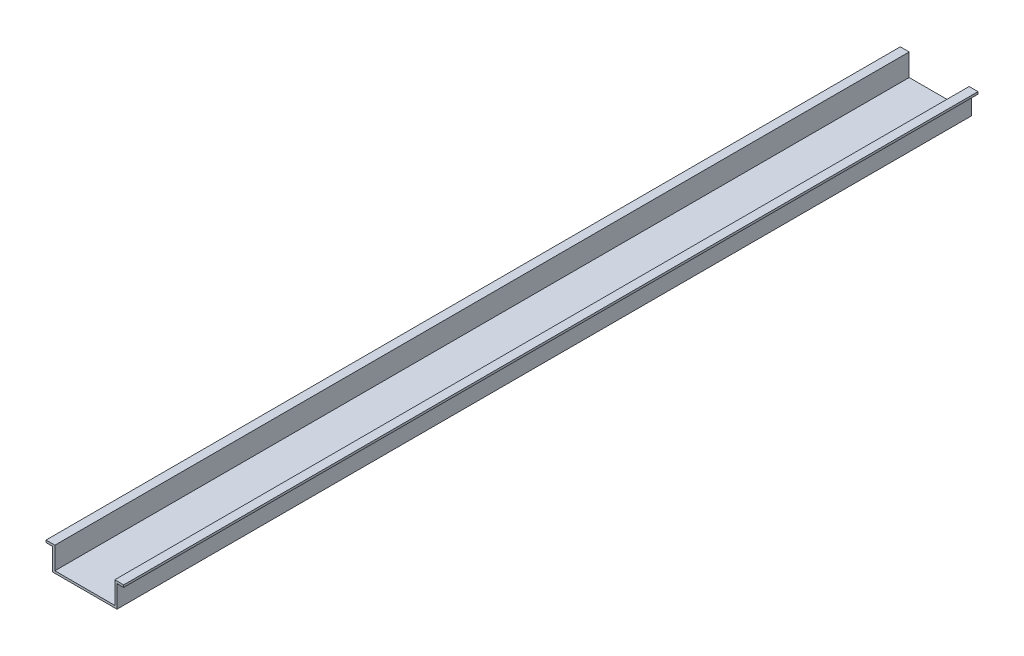
SolidWorks part; units mm, degrees
ref_plane "Front Plane" through (0, 0, 0) normal (0, 0, 1) x (1, 0, 0)
ref_plane "Top Plane" through (0, 0, 0) normal (0, 1, 0) x (1, 0, 0)
ref_plane "Right Plane" through (0, 0, 0) normal (1, 0, 0) x (0, 0, -1)
sketch "Sketch1" plane through (0, 0, 0) normal (0, 0, 1) x (1, 0, 0)
  line L0 (-17.5, 10) -> (-13.5, 10)
  line L1 (-13.5, 10) -> (-13.5, 0)
  line L2 (-13.5, 0) -> (13.5, 0)
  line L3 (13.5, 0) -> (13.5, 10)
  line L4 (13.5, 10) -> (17.5, 10)
  line L5 (-17.5, 9) -> (-14.5, 9)
  line L6 (-14.5, 9) -> (-14.5, -1)
  line L7 (-14.5, -1) -> (14.5, -1)
  line L8 (14.5, -1) -> (14.5, 9)
  line L9 (14.5, 9) -> (17.5, 9)
  line L10 (-17.5, 10) -> (-17.5, 9)
  line L11 (17.5, 10) -> (17.5, 9)
  point P5 (0, 0)
  dimension "D1" = 10
  dimension "D3" = 35
  dimension "D4" = 4
  dimension "D2" = 1
extrude "Boss-Extrude1" add sketch "Sketch1" along normal blind 385
